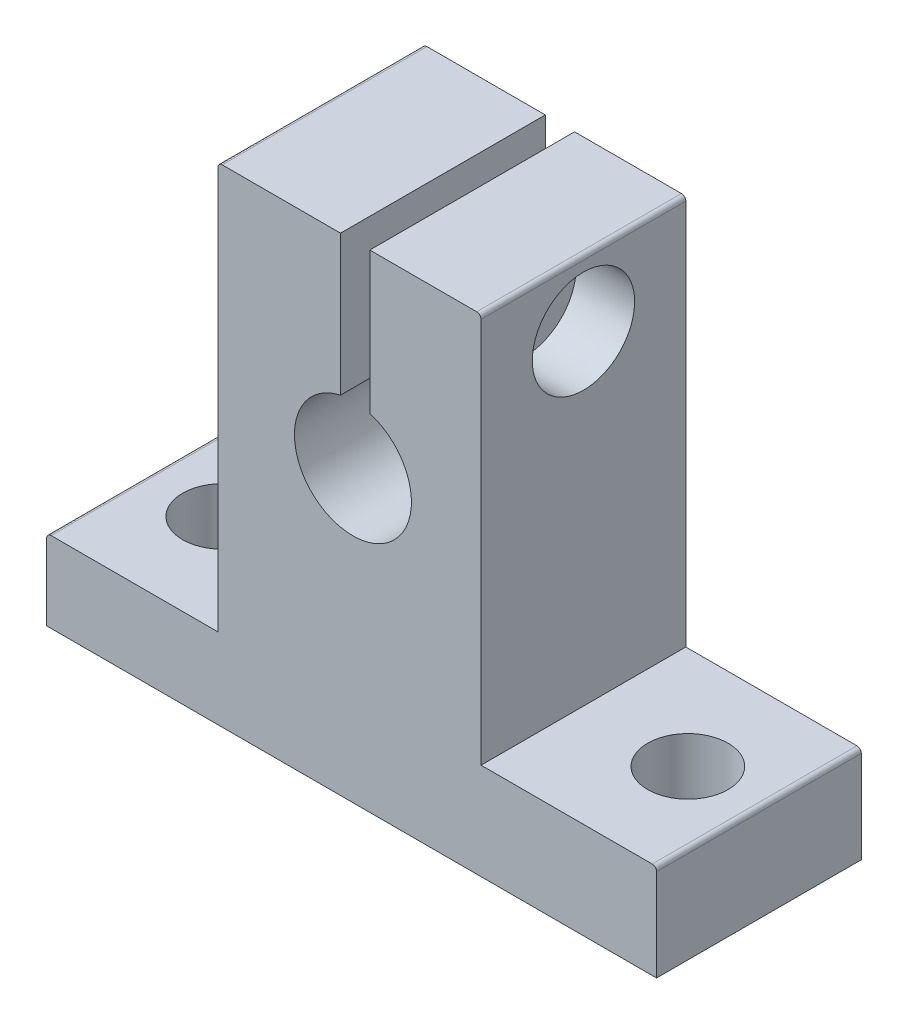
SolidWorks part; units mm, degrees
ref_plane "Front Plane" through (0, 0, 0) normal (0, 0, 1) x (1, 0, 0)
ref_plane "Top Plane" through (0, 0, 0) normal (0, 1, 0) x (1, 0, 0)
ref_plane "Right Plane" through (0, 0, 0) normal (1, 0, 0) x (0, 0, -1)
sketch "Sketch1" plane through (0, 0, 0) normal (0, 0, 1) x (1, 0, 0)
  line L1 (-20.9389, 0.7864) -> (-9.2389, 0.7864)
  line L2 (-20.9389, 0.7864) -> (-20.9389, -4.7136)
  line L3 (-20.9389, -4.7136) -> (20.7611, -4.7136)
  line L4 (20.7611, 1.8864) -> (20.7611, -4.7136)
  line L7 (-9.2389, 28.5864) -> (8.7611, 28.5864)
  line L8 (-9.2389, 28.5864) -> (-9.2389, 0.7864)
  line L9 (8.7611, 1.8864) -> (20.7611, 1.8864)
  line L10 (8.7611, 28.5864) -> (8.7611, 1.8864)
  circle A0 centre (0, 15.0864) radius 4
  point P0 (0, 0)
  point P6 (0, 0)
  dimension "D7" = 8
  dimension "D1" = 33.3
  dimension "D2" = 41.7
  dimension "D3" = 18
  dimension "D4" = 12
  dimension "D5" = 6.6
  dimension "D6" = 5.5
  dimension "D8" = 19.8
extrude "Boss-Extrude1" add sketch "Sketch1" along normal blind 14
sketch "Sketch2" plane through (0, 1.8864, 0) normal (0, 1, 0) x (1, 0, 0)
  line L0 (20.7611, -14) -> (8.7611, -14) construction
  line L1 (-9.2389, -14) -> (-20.9389, -14) construction
  circle A0 centre (-15.9, -7) radius 2.75
  circle A1 centre (15.9, -7) radius 2.75
  point P4 (14.7611, -14)
  dimension "D1" = 5.5
  dimension "D2" = 5.5
  dimension "D3" = 7
  dimension "D4" = 7
  dimension "D5" = 31.8
  dimension "D6" = 15.9
extrude "Cut-Extrude1" cut sketch "Sketch2" against normal blind 6
sketch "Sketch3" plane through (0, 0, 14) normal (0, 0, 1) x (1, 0, 0)
  line L1 (-0.8474, 29.683) -> (1.1526, 29.683)
  line L2 (-0.8474, 29.683) -> (-0.8474, 18.0622)
  line L3 (-0.8474, 18.0622) -> (1.1526, 18.0622)
  line L4 (1.1526, 29.683) -> (1.1526, 18.0622)
  line L5 (-0.8474, 29.683) -> (1.1526, 18.0622) construction
  line L6 (-0.8474, 18.0622) -> (1.1526, 29.683) construction
  point P0 (0.1526, 23.8726)
  dimension "D1" = 2
extrude "Cut-Extrude2" cut sketch "Sketch3" against normal blind 14
sketch "Sketch4" plane through (8.7611, 0, 0) normal (1, 0, 0) x (0, 0, -1)
  line L0 (0, 1.8864) -> (0, 28.5864) construction
  line L2 (-14, 28.5864) -> (0, 28.5864) construction
  circle A0 centre (-7, 24.0864) radius 2
  dimension "D1" = 4
  dimension "D2" = 7
  dimension "D3" = 4.5
extrude "Cut-Extrude3" cut sketch "Sketch4" against normal blind 9
sketch "Sketch5" plane through (8.7611, 0, 0) normal (1, 0, 0) x (0, 0, -1)
  circle A0 centre (-7, 24.0864) radius 3.5
  dimension "D1" = 7
extrude "Cut-Extrude4" cut sketch "Sketch5" against normal blind 4
sketch "Sketch6" plane through (-9.2389, 0, 0) normal (-1, 0, 0) x (0, 0, 1)
  line L0 (14, 28.5864) -> (14, 0.7864) construction
  line L1 (14, 28.5864) -> (0, 28.5864) construction
  circle A0 centre (7, 24.0864) radius 1.85
  point P4 (7, 28.5864)
  dimension "D1" = 3.7
  dimension "D2" = 7
  dimension "D3" = 4.5
extrude "Cut-Extrude5" cut sketch "Sketch6" against normal blind 9
fillet "Fillet1" radius 0.3 4 edges at (-9.2389, 28.5864, 7) (8.7611, 28.5864, 7) (-20.9389, 0.7864, 7) (20.7611, 1.8864, 7)
